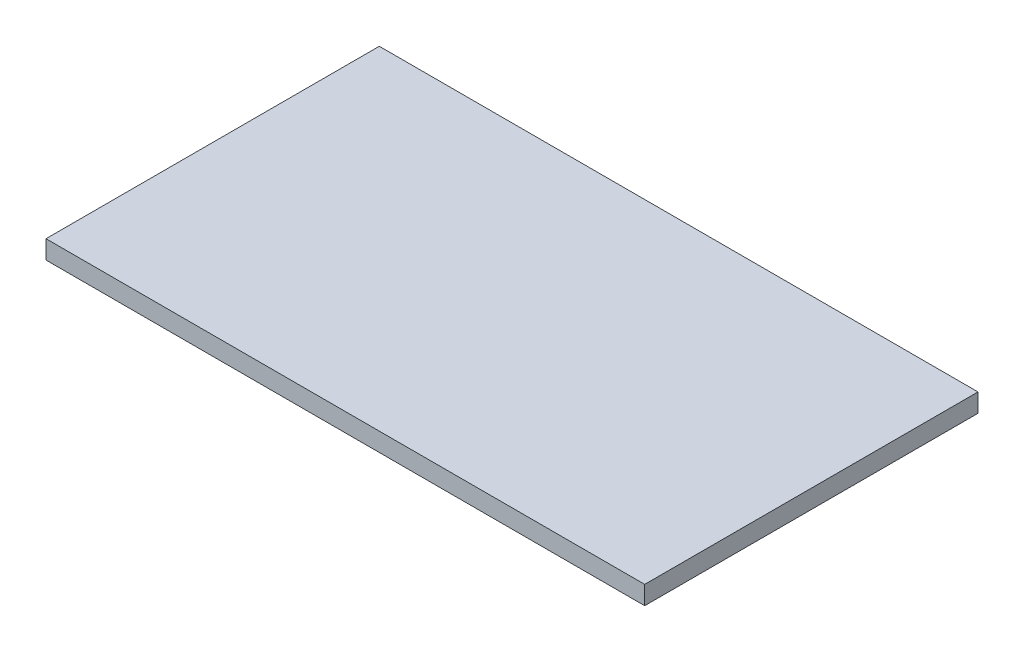
SolidWorks part; units mm, degrees
ref_plane "Plano frontal" through (0, 0, 0) normal (0, 0, 1) x (1, 0, 0)
ref_plane "Plano superior" through (0, 0, 0) normal (0, 1, 0) x (1, 0, 0)
ref_plane "Plano direito" through (0, 0, 0) normal (1, 0, 0) x (0, 0, -1)
sketch "Esboço1" plane through (0, 0, 0) normal (0, 0, 1) x (1, 0, 0)
  line L1 (0, 0) -> (4850, 0)
  line L2 (0, 0) -> (0, 150)
  line L3 (0, 150) -> (4850, 150)
  line L4 (4850, 0) -> (4850, 150)
  dimension "D1" = 150
  dimension "D2" = 4850
extrude "Ressalto-extrusão1" add sketch "Esboço1" along normal blind 2700
